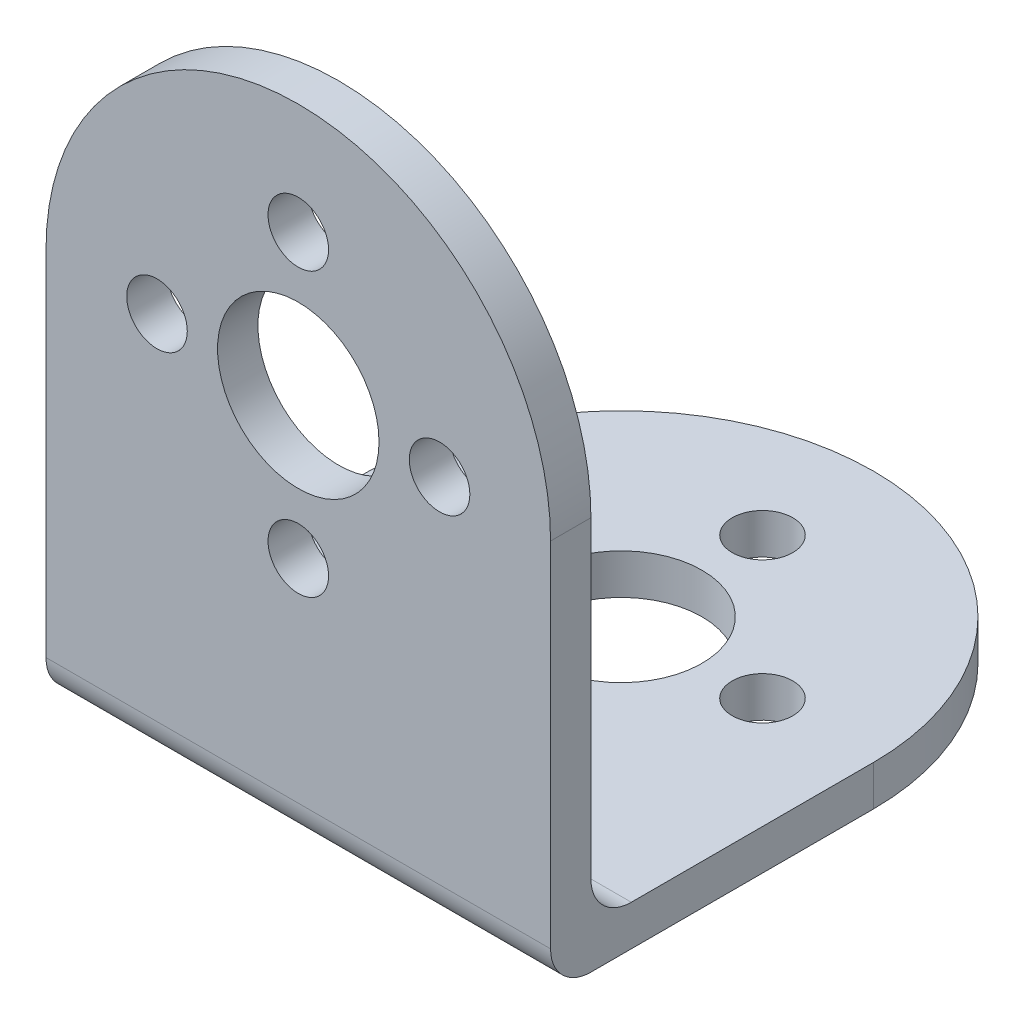
SolidWorks part; units mm, degrees
ref_plane "Front Plane" through (0, 0, 0) normal (0, 0, 1) x (1, 0, 0)
ref_plane "Top Plane" through (0, 0, 0) normal (0, 1, 0) x (1, 0, 0)
ref_plane "Right Plane" through (0, 0, 0) normal (1, 0, 0) x (0, 0, -1)
sketch "Sketch1" plane through (0, 0, 0) normal (0, 0, 1) x (1, 0, 0)
  line L0 (0, 15.4194) -> (0, -17.763) construction
  line L1 (-15.3609, 0) -> (24.5268, 0) construction
  line L2 (-12.5, 0) -> (-12.5, -19.5)
  line L3 (-12.5, -19.5) -> (12.5, -19.5)
  line L4 (12.5, -19.5) -> (12.5, 0)
  arc A0 (12.5, 0) -> (-12.5, 0) centre (0, 0) ccw
  circle A1 centre (0, 0) radius 4
  circle A2 centre (0, 0) radius 7 construction
  circle A3 centre (0, 7) radius 1.5
  circle A4 centre (7, 0) radius 1.5
  circle A5 centre (0, -7) radius 1.5
  circle A6 centre (-7, 0) radius 1.5
  point P20 (0, 0)
  dimension "D1" = 25
  dimension "D2" = 8
  dimension "D3" = 14
  dimension "D4" = 3
  dimension "D6" = 19.5
  dimension "D5" = 4
extrude "Boss-Extrude1" add sketch "Sketch1" against normal blind 2
sketch "Sketch2" plane through (0, -19.5, 0) normal (0, -1, 0) x (1, 0, 0)
  line L0 (0, 3.3482) -> (0, -28.5454) construction
  line L1 (-17.1084, -16) -> (13.5481, -16) construction
  line L2 (-12.5, -16) -> (-12.5, 0)
  line L8 (-12.5, 0) -> (12.5, 0)
  line L9 (12.5, 0) -> (12.5, -16)
  circle A0 centre (0, -16) radius 4
  circle A1 centre (0, -16) radius 7 construction
  arc A3 (-12.5, -16) -> (12.5, -16) centre (0, -16) ccw
  circle A4 centre (0, -9) radius 1.5
  circle A5 centre (7, -16) radius 1.5
  circle A6 centre (0, -23) radius 1.5
  circle A7 centre (-7, -16) radius 1.5
  point P27 (0, -16)
  dimension "D1" = 8
  dimension "D2" = 14
  dimension "D3" = 16
  dimension "D4" = 25
  dimension "D5" = 3
  dimension "D6" = 4
extrude "Boss-Extrude2" add sketch "Sketch2" against normal blind 2
fillet "Fillet1" radius 2 2 edges at (0, -19.5, 0) (0, -17.5, -2)
